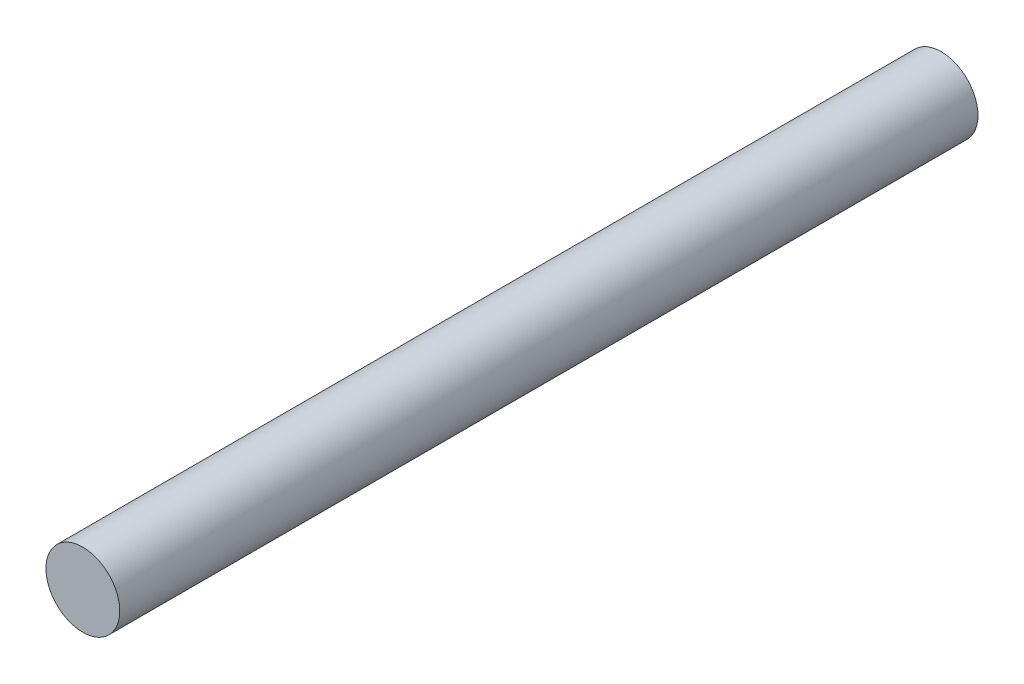
SolidWorks part; units mm, degrees
ref_plane "Front Plane" through (0, 0, 0) normal (0, 0, 1) x (1, 0, 0)
ref_plane "Top Plane" through (0, 0, 0) normal (0, 1, 0) x (1, 0, 0)
ref_plane "Right Plane" through (0, 0, 0) normal (1, 0, 0) x (0, 0, -1)
sketch "Sketch1" plane through (0, 0, 0) normal (0, 0, 1) x (1, 0, 0)
  circle A0 centre (0, 0) radius 10.922
  dimension "D1" = 21.844
extrude "Boss-Extrude1" add sketch "Sketch1" along normal blind 254
